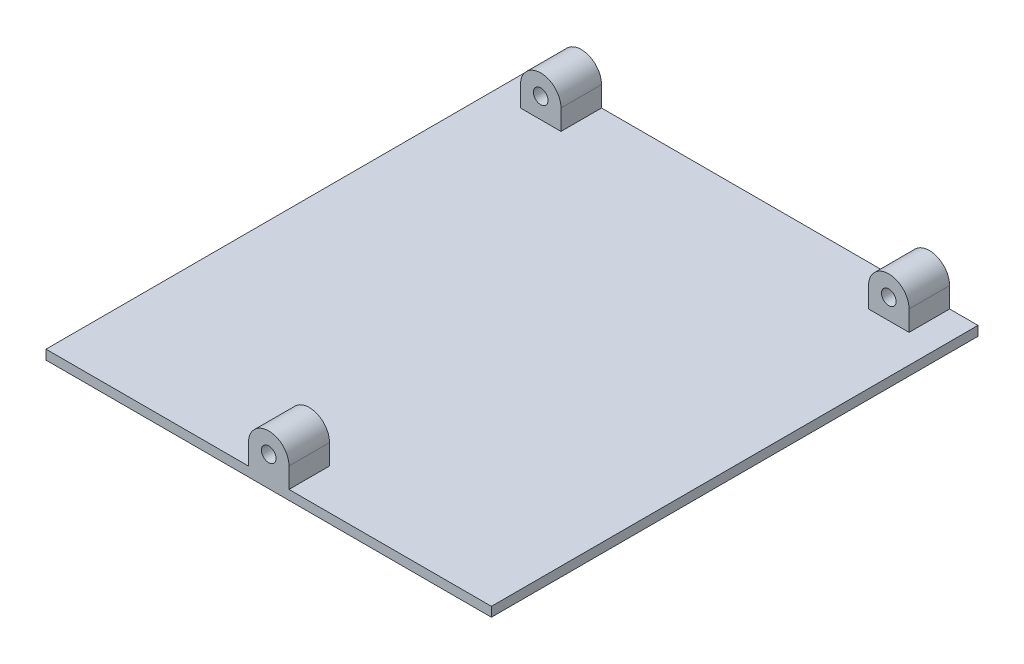
SolidWorks part; units mm, degrees
ref_plane "Front Plane" through (0, 0, 0) normal (0, 0, 1) x (1, 0, 0)
ref_plane "Top Plane" through (0, 0, 0) normal (0, 1, 0) x (1, 0, 0)
ref_plane "Right Plane" through (0, 0, 0) normal (1, 0, 0) x (0, 0, -1)
sketch "Sketch1" plane through (0, 0, 0) normal (0, 1, 0) x (1, 0, 0)
  line L1 (0, 0) -> (139.5, 0)
  line L2 (0, 0) -> (0, 152.4)
  line L3 (0, 152.4) -> (139.5, 152.4)
  line L4 (139.5, 0) -> (139.5, 152.4)
  dimension "D1" = 152.4
  dimension "D2" = 139.5
extrude "Boss-Extrude1" add sketch "Sketch1" along normal blind 6.35
sketch "Sketch2" plane through (0, 6.35, 0) normal (0, 1, 0) x (1, 0, 0)
  line L0 (0, 0) -> (139.5, 0) construction
  line L1 (0, 152.4) -> (139.5, 152.4)
  line L2 (0, 152.4) -> (0, 0)
  line L3 (0, 0) -> (139.5, 0)
  line L4 (139.5, 152.4) -> (139.5, 0)
  line L5 (139.5, 0) -> (139.5, 152.4) construction
extrude "Cut-Extrude1" cut sketch "Sketch2" against normal blind 3.375
sketch "Sketch3" plane through (0, 0, 0) normal (0, 0, 1) x (1, 0, 0)
  line L0 (63.4, 9.325) -> (63.4, 2.975)
  line L1 (63.4, 2.975) -> (76.1, 2.975)
  line L2 (76.1, 9.325) -> (76.1, 2.975)
  line L3 (0, 2.975) -> (139.5, 2.975) construction
  arc A0 (76.1, 9.325) -> (63.4, 9.325) centre (69.75, 9.325) ccw
  circle A1 centre (69.75, 9.325) radius 2.286
  point P6 (69.75, 2.975)
  point P9 (69.75, 2.975)
  dimension "D1" = 4.572
  dimension "D2" = 12.7
  dimension "D8" = 6.35
  dimension "D5" = 6.35
extrude "Boss-Extrude2" add sketch "Sketch3" against normal blind 12.7
sketch "Sketch4" plane through (0, 0, -152.4) normal (0, 0, -1) x (-1, 0, 0)
  line L0 (-130.61, 9.325) -> (-130.61, 2.975)
  line L1 (-130.61, 2.975) -> (-117.91, 2.975)
  line L2 (-117.91, 9.325) -> (-117.91, 2.975)
  line L3 (-21.59, 9.325) -> (-21.59, 2.975)
  line L4 (-21.59, 2.975) -> (-8.89, 2.975)
  line L5 (-8.89, 9.325) -> (-8.89, 2.975)
  line L6 (-139.5, 2.975) -> (0, 2.975) construction
  line L7 (0, 2.975) -> (0, 0) construction
  line L8 (-139.5, 2.975) -> (-139.5, 0) construction
  arc A0 (-117.91, 9.325) -> (-130.61, 9.325) centre (-124.26, 9.325) ccw
  circle A1 centre (-124.26, 9.325) radius 2.286
  arc A2 (-8.89, 9.325) -> (-21.59, 9.325) centre (-15.24, 9.325) ccw
  circle A3 centre (-15.24, 9.325) radius 2.286
  dimension "D1" = 4.572
  dimension "D3" = 6.35
  dimension "D5" = 4.572
  dimension "D7" = 6.35
  dimension "D2" = 6.35
  dimension "D4" = 12.7
  dimension "D6" = 6.35
  dimension "D8" = 12.7
  dimension "D9" = 8.89
  dimension "D10" = 8.89
  dimension "D11" = 15.24
  dimension "D12" = 15.24
extrude "Boss-Extrude3" add sketch "Sketch4" against normal blind 12.7
